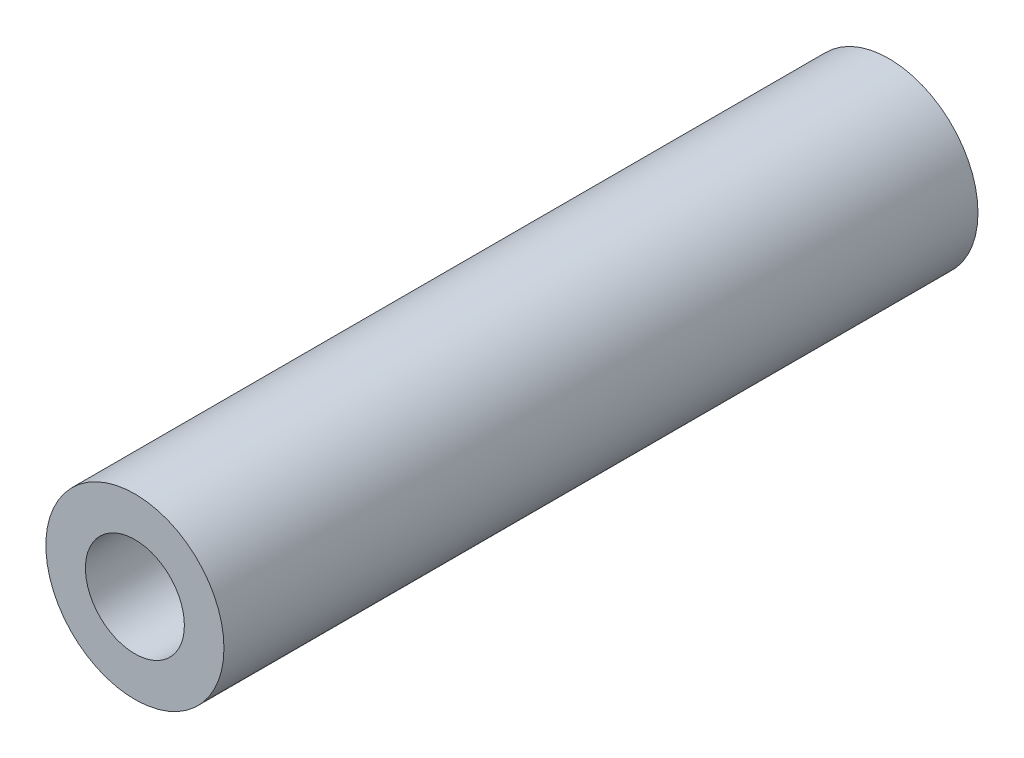
SolidWorks part; units mm, degrees
ref_plane "Front Plane" through (0, 0, 0) normal (0, 0, 1) x (1, 0, 0)
ref_plane "Top Plane" through (0, 0, 0) normal (0, 1, 0) x (1, 0, 0)
ref_plane "Right Plane" through (0, 0, 0) normal (1, 0, 0) x (0, 0, -1)
sketch "Sketch1" plane through (0, 0, 0) normal (0, 0, 1) x (1, 0, 0)
  circle A0 centre (0, 0) radius 0.9
  circle A1 centre (0, 0) radius 0.5
  dimension "D1" = 1.8
  dimension "D2" = 1
extrude "Boss-Extrude1" add sketch "Sketch1" along normal blind 7.62 contours A0
